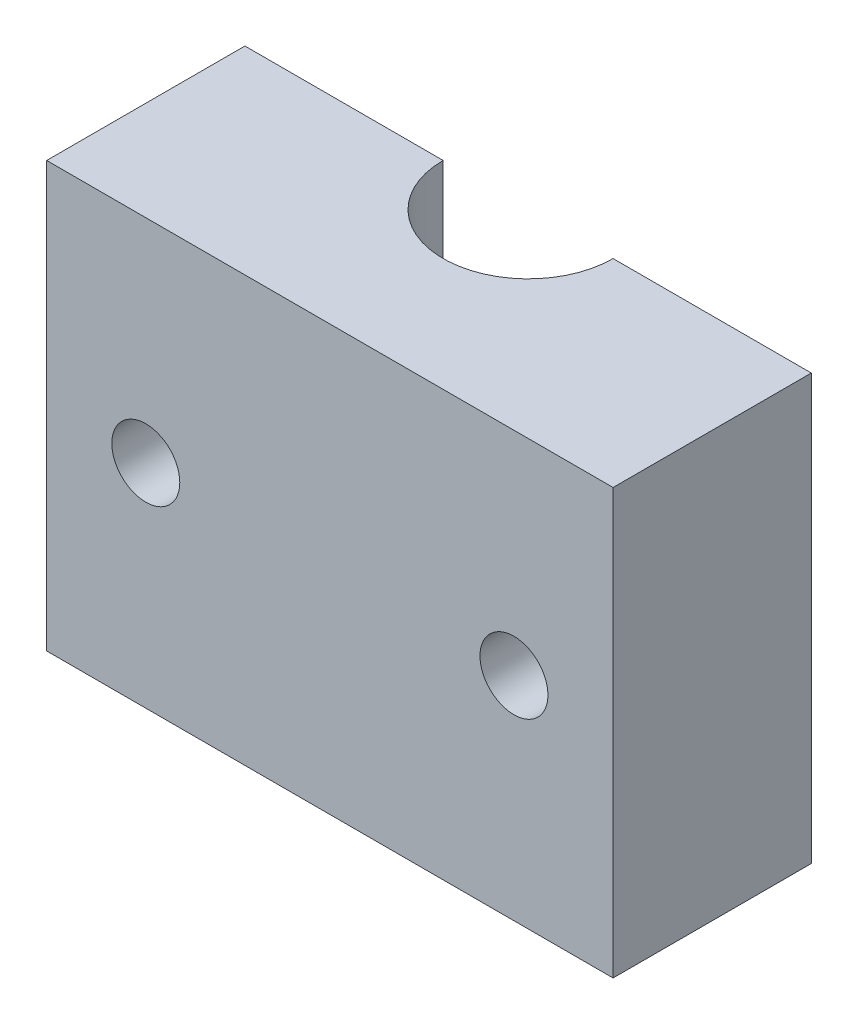
SolidWorks part; units mm, degrees
material "Náilon 6/10"
ref_plane "Front" through (0, 0, 0) normal (0, 0, 1) x (1, 0, 0)
ref_plane "Top" through (0, 0, 0) normal (0, 1, 0) x (1, 0, 0)
ref_plane "Right" through (0, 0, 0) normal (1, 0, 0) x (0, 0, -1)
sketch "Sketch1" plane through (0, 0, 0) normal (0, 0, 1) x (1, 0, 0)
  line L0 (10, -7.5) -> (-10, 7.5) construction
  line L1 (-10, 7.5) -> (10, 7.5)
  line L2 (-10, 7.5) -> (-10, -7.5)
  line L3 (-10, -7.5) -> (10, -7.5)
  line L4 (10, 7.5) -> (10, -7.5)
  dimension "D1" = 20
  dimension "D2" = 15
extrude "Extrude1" add sketch "Sketch1" along normal mid plane 7
sketch "Sketch2" plane through (0, 7.5, 0) normal (0, 1, 0) x (-1, 0, 0)
  line L0 (-10, -3.5) -> (10, -3.5) construction
  circle A0 centre (0, -3.5) radius 3
  dimension "D1" = 6
extrude "Cut-Extrude1" cut sketch "Sketch2" against normal through all
sketch "Sketch3" plane through (0, 0, 3.5) normal (0, 0, 1) x (1, 0, 0)
  line L0 (10, 7.5) -> (-10, 7.5) construction
  line L1 (-10, -7.5) -> (10, -7.5) construction
  circle A0 centre (-6.5, 0) radius 1.2
  circle A1 centre (6.5, 0) radius 1.2
  dimension "D1" = 2.4
  dimension "D2" = 2.4
  dimension "D3" = 6.5
  dimension "D4" = 13
  dimension "D5" = 7.5
  dimension "D6" = 7.5
extrude "Cut-Extrude2" cut sketch "Sketch3" against normal through all
cosmetic thread "Cosmetic Thread1" parameters "D2"=3
cosmetic thread "Cosmetic Thread2" parameters "D2"=3
